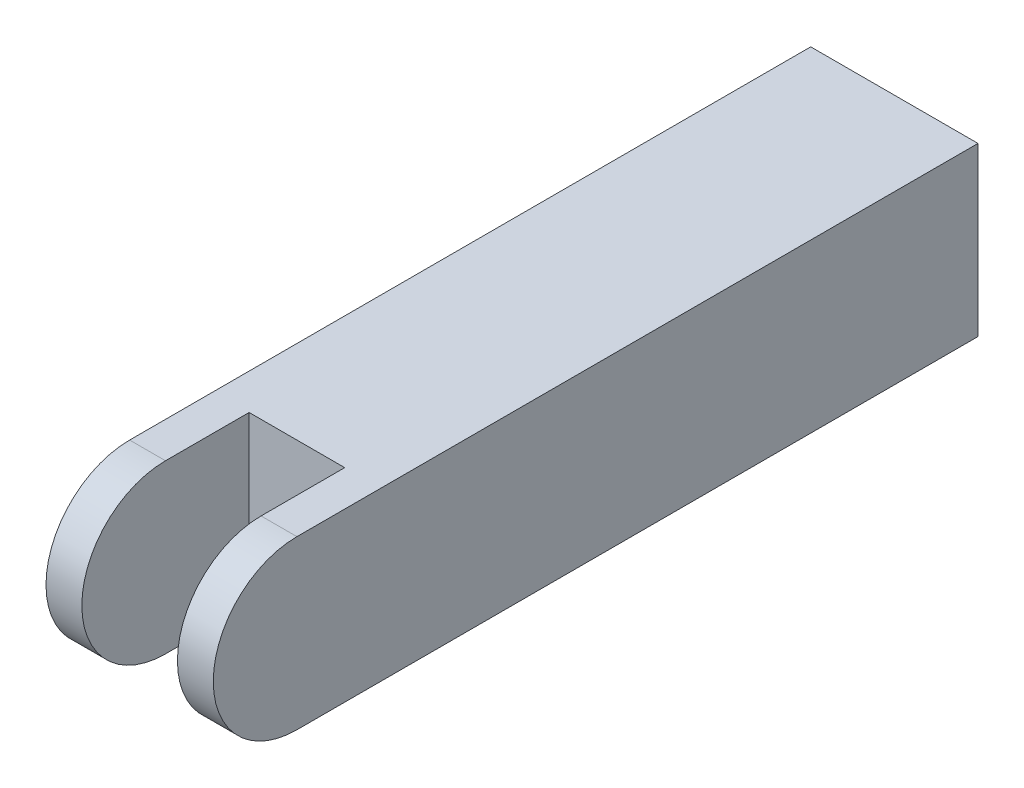
SolidWorks part; units mm, degrees
ref_plane "Front" through (0, 0, 0) normal (0, 0, 1) x (1, 0, 0)
ref_plane "Top" through (0, 0, 0) normal (0, 1, 0) x (1, 0, 0)
ref_plane "Right" through (0, 0, 0) normal (1, 0, 0) x (0, 0, -1)
sketch "草图1" plane through (0, 0, 0) normal (0, 0, 1) x (1, 0, 0)
  line L0 (-23.0785, 0) -> (0, 0) construction
  line L1 (-7, 7) -> (7, 7)
  line L2 (-7, 7) -> (-7, -7)
  line L3 (-7, -7) -> (7, -7)
  line L4 (7, 7) -> (7, -7)
  line L5 (0, 0) -> (0, 32.9454) construction
  dimension "D1" = 14
  dimension "D2" = 14
  dimension "D3" = 7
  dimension "D4" = 7
extrude "凸台-拉伸1" add sketch "草图1" along normal blind 64
sketch "草图2" plane through (7, 0, 0) normal (1, 0, 0) x (0, 0, -1)
  line L1 (-57, 7) -> (-68.5468, 7)
  line L3 (-57, -7) -> (-68.5468, -7)
  line L4 (-68.5468, 7) -> (-68.5468, -7)
  arc A0 (-57, 7) -> (-57, -7) centre (-57, 0) ccw
extrude "切除-拉伸1" cut sketch "草图2" against normal blind 64
sketch "草图3" plane through (0, 7, 0) normal (0, 1, 0) x (1, 0, 0)
  line L0 (0, -57) -> (0, -70.6964) construction
  line L1 (-7, -57) -> (7, -57) construction
  line L2 (-7, -64) -> (7, -64) construction
  line L4 (-4, -64) -> (4, -64)
  line L5 (-4, -64) -> (-4, -50)
  line L6 (-4, -50) -> (4, -50)
  line L7 (4, -64) -> (4, -50)
  dimension "D1" = 8
  dimension "D2" = 4
  dimension "D3" = 14
extrude "切除-拉伸2" cut sketch "草图3" against normal through all
